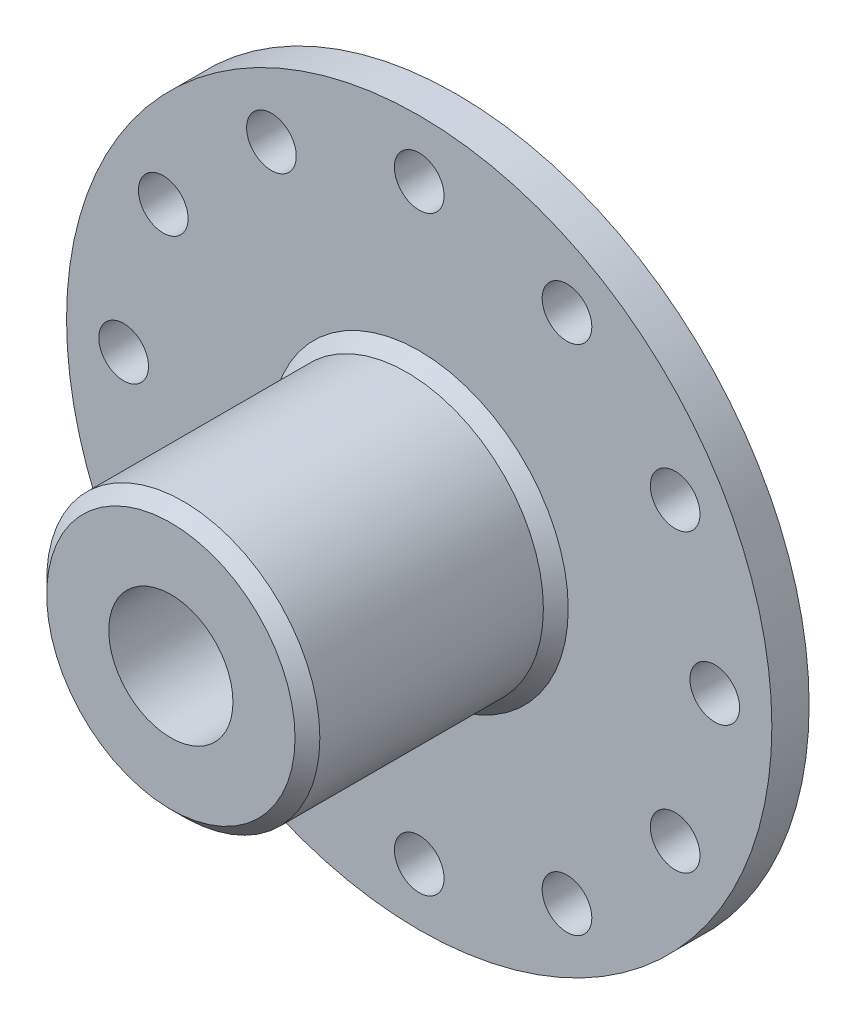
SolidWorks part; units mm, degrees
ref_plane "Front Plane" through (0, 0, 0) normal (0, 0, 1) x (1, 0, 0)
ref_plane "Top Plane" through (0, 0, 0) normal (0, 1, 0) x (1, 0, 0)
ref_plane "Right Plane" through (0, 0, 0) normal (1, 0, 0) x (0, 0, -1)
sketch "Sketch1" plane through (0, 0, 0) normal (0, 0, 1) x (1, 0, 0)
  circle A0 centre (0, 0) radius 28.4
  circle A1 centre (0, 0) radius 28.4 construction
extrude "Boss-Extrude1" add sketch "Sketch1" along normal blind 3
sketch "Sketch2" plane through (0, 0, 3) normal (0, 0, 1) x (1, 0, 0)
  circle A0 centre (0, 0) radius 11
  dimension "D1" = 22
extrude "Boss-Extrude2" add sketch "Sketch2" along normal blind 20
sketch "Sketch3" plane through (0, 0, 23) normal (0, 0, 1) x (1, 0, 0)
  circle A0 centre (0, 0) radius 5
  dimension "D1" = 10
extrude "Cut-Extrude1" cut sketch "Sketch3" against normal through all
sketch "Sketch4" plane through (0, 0, 0) normal (0, 1, 0) x (1, 0, 0)
  circle A0 centre (0, -15) radius 2
  dimension "D1" = 4
  dimension "D2" = 15
extrude "Cut-Extrude2" cut sketch "Sketch4" against normal blind 15
chamfer "Chamfer1" distance 1 angle 45 2 edges at (11, 0, 3) (11, 0, 23)
sketch "Sketch5" plane through (0, 0, 3) normal (0, 0, 1) x (1, 0, 0)
  circle A0 centre (11.9, 20.6114) radius 2
  circle A1 centre (0, 0) radius 28.4
  circle A2 centre (0, 0) radius 28.4
  dimension "D2" = 4
  dimension "D1" = 0
extrude "Cut-Extrude5" cut sketch "Sketch5" against normal through all contours A0
pattern_circular "CirPattern2" count 12 over 360 about axis through (0, 0, 0) along (0, 0, 1) of "Cut-Extrude5"
